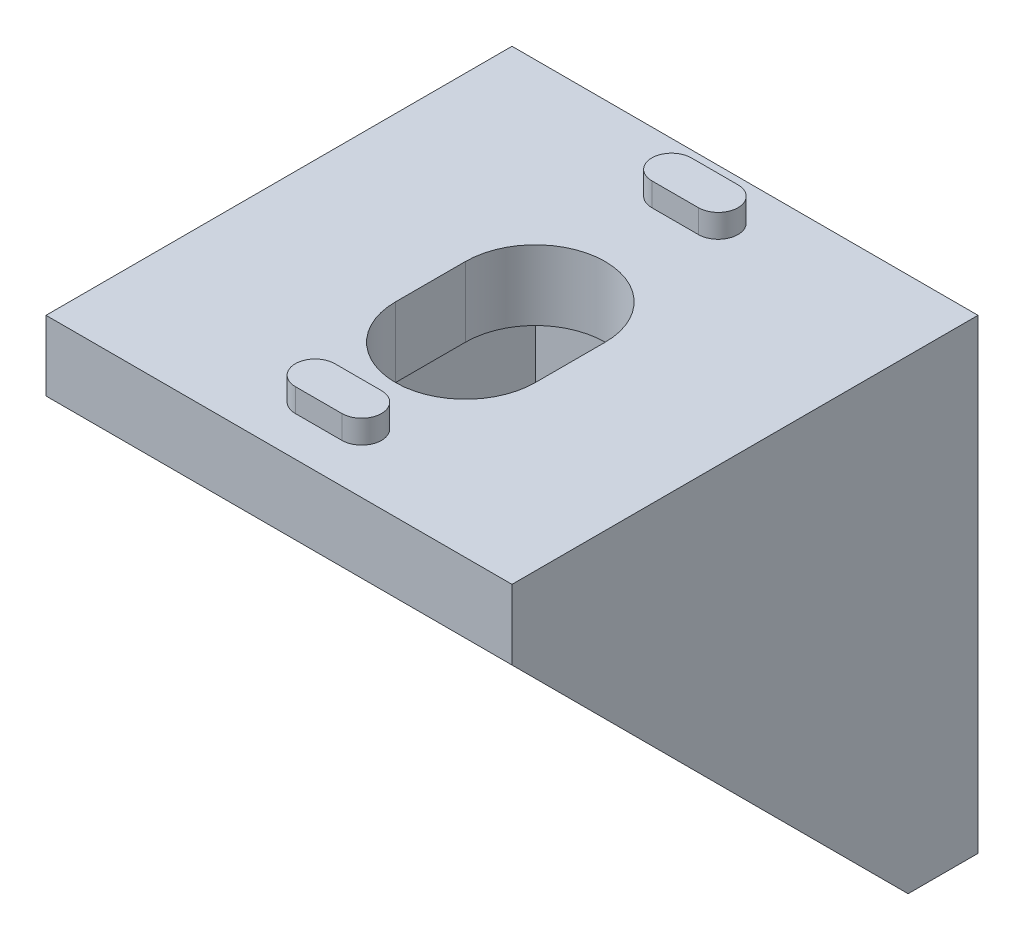
SolidWorks part; units mm, degrees
material "1060 Alloy"
ref_plane "Front Plane" through (0, 0, 0) normal (0, 0, 1) x (1, 0, 0)
ref_plane "Top Plane" through (0, 0, 0) normal (0, 1, 0) x (1, 0, 0)
ref_plane "Right Plane" through (0, 0, 0) normal (1, 0, 0) x (0, 0, -1)
sketch "Sketch1" plane through (0, 0, 0) normal (1, 0, 0) x (0, 0, -1)
  line L0 (0, 0) -> (-20, 0)
  line L1 (-20, 0) -> (-20, -3)
  line L2 (-20, -3) -> (-11.5, -11.5)
  line L3 (-11.5, -11.5) -> (0, 0) construction
  line L4 (-3, -20) -> (-11.5, -11.5)
  line L5 (0, -20) -> (-3, -20)
  line L6 (0, 0) -> (0, -20)
  dimension "D1" = 3
  dimension "D2" = 20
extrude "Boss-Extrude1" add sketch "Sketch1" along normal mid plane 20
sketch "Sketch2" plane through (0, 0, 0) normal (1, 0, 0) x (0, 0, -1)
  line L0 (-20, -3) -> (-3, -20) construction
  line L1 (-3, -3) -> (-20, -3)
  line L2 (-3, -3) -> (-3, -20)
  line L3 (-3, -20) -> (-20, -20)
  line L4 (-20, -3) -> (-20, -20)
  line L5 (-20, 0) -> (-20, -3) construction
extrude "Cut-Extrude1" cut sketch "Sketch2" against normal mid plane 12
sketch "Sketch3" plane through (0, 0, 3) normal (0, 0, 1) x (1, 0, 0)
  line L0 (0, -9) -> (0, -12) construction
  line L1 (-3, -9) -> (-3, -12)
  line L2 (3, -9) -> (3, -12)
  line L3 (0, -10.5) -> (0.7454, -10.5) construction
  line L4 (-6, -20) -> (6, -20) construction
  arc A0 (-3, -9) -> (3, -9) centre (0, -9) cw
  arc A1 (-3, -12) -> (3, -12) centre (0, -12) ccw
  dimension "D3" = 9
  dimension "D4" = 5
  dimension "D1" = 3
  dimension "D2" = 3
extrude "Cut-Extrude2" cut sketch "Sketch3" against normal up to next (3 mm away)
sketch "Sketch4" plane through (0, 0, 0) normal (0, 0, -1) x (-1, 0, 0)
  line L0 (-1, -2.15) -> (1, -2.15) construction
  line L1 (-1, -3) -> (1, -3)
  line L2 (-1, -1.3) -> (1, -1.3)
  line L3 (0, 0) -> (0, -2.15) construction
  line L4 (-10, 0) -> (10, 0) construction
  line L5 (-2.1032, -9.8) -> (3, -9.8) construction
  line L6 (-1, -18.3) -> (1, -18.3)
  line L7 (-1, -16.6) -> (1, -16.6)
  line L8 (3, -12) -> (3, -9) construction
  arc A0 (-1, -3) -> (-1, -1.3) centre (-1, -2.15) cw
  arc A1 (1, -3) -> (1, -1.3) centre (1, -2.15) ccw
  arc A2 (1, -16.6) -> (1, -18.3) centre (1, -17.45) cw
  arc A3 (-1, -16.6) -> (-1, -18.3) centre (-1, -17.45) ccw
  dimension "D3" = 3.7
  dimension "D4" = 3
  dimension "D5" = 17
  dimension "D1" = 0.85
  dimension "D2" = 0.85
extrude "Boss-Extrude2" add sketch "Sketch4" along normal blind 1
ref_plane "Plane1" through (0, 0, 0) normal (0, 0.7071, 0.7071) x (-1, 0, 0)
mirror "Mirror1" about plane through (0, 0, 0) normal (0, 0.7071, 0.7071) of "Boss-Extrude2", "Cut-Extrude2"
